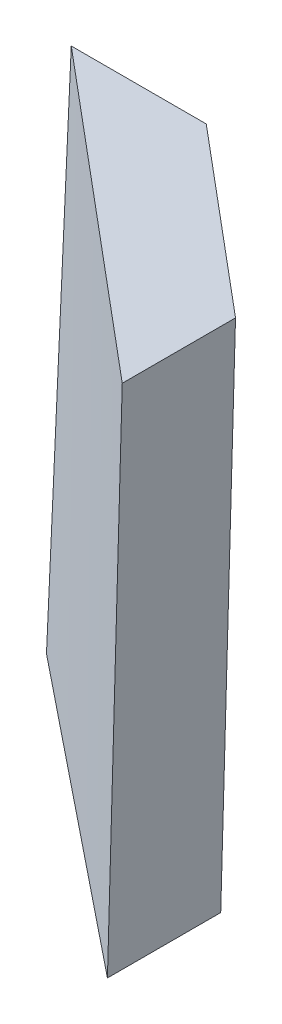
SolidWorks part; units mm, degrees
ref_plane "Alzado" through (0, 0, 0) normal (0, 0, 1) x (1, 0, 0)
ref_plane "Planta" through (0, 0, 0) normal (0, 1, 0) x (1, 0, 0)
ref_plane "Vista lateral" through (0, 0, 0) normal (1, 0, 0) x (0, 0, -1)
sketch "Croquis1" plane through (0, 0, 0) normal (0, 1, 0) x (1, 0, 0)
  line L0 (0, 0) -> (19.45, 0)
  line L1 (19.45, 0) -> (44.8553, -19.7515)
  line L2 (44.8553, -19.7515) -> (44.8553, -36.0715)
  line L3 (44.8553, -36.0715) -> (0, 0)
  point P3 (30.0769, -6.4766)
  point P6 (0, 0)
  point P7 (0, 0)
  dimension "D1" = 19.45
  dimension "D2" = 16.32
  dimension "D3" = 57.56
  dimension "D4" = 32.18
ref_plane "Plano1" through (0, 75, 0) normal (0, 1, 0) x (1, 0, 0)
sketch "Croquis2" plane through (0, 75, 0) normal (0, 1, 0) x (1, 0, 0)
  line L0 (0.95, 2.62) -> (20.4, 2.62)
  line L1 (20.4, 2.62) -> (46.7061, -19.4687)
  line L2 (46.7061, -19.4687) -> (46.7061, -35.7889)
  line L3 (46.7061, -35.7889) -> (0.95, 2.62)
  line L4 (19.45, 0) -> (19.45, 2.62) construction
  line L5 (19.45, 2.62) -> (20.4, 2.62) construction
  point P7 (0, 0)
  point P10 (0, 0)
  point P11 (0, 0)
  point P12 (0, 0)
  dimension "D1" = 19.45
  dimension "D2" = 12.5
  dimension "D3" = 59.74
  dimension "D4" = 34.35
  dimension "D5" = 2.62
  dimension "D6" = 0.95
loft "Recubrir1" add profiles "Croquis1", "Croquis2"
